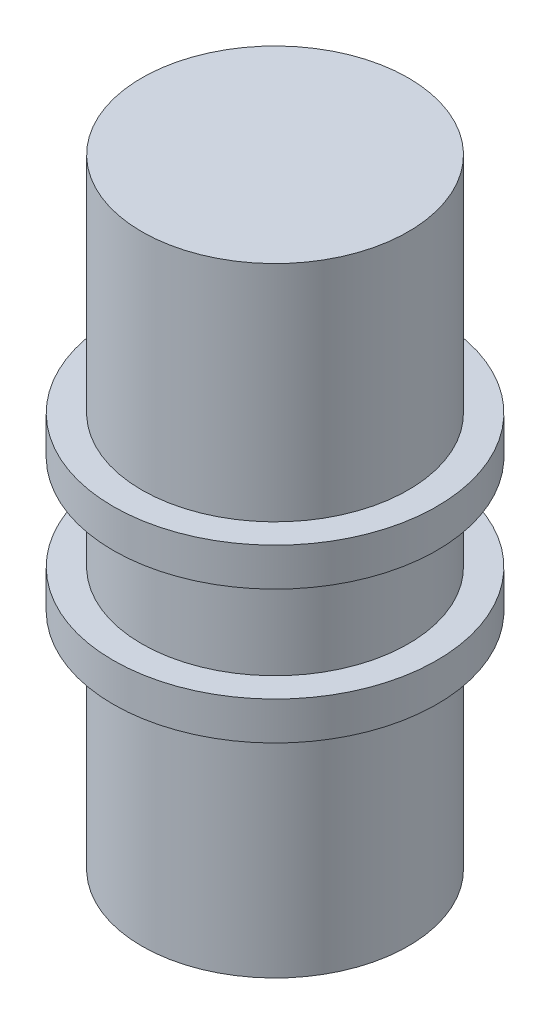
SolidWorks part; units mm, degrees
ref_plane "前视基准面" through (0, 0, 0) normal (0, 0, 1) x (1, 0, 0)
ref_plane "上视基准面" through (0, 0, 0) normal (0, 1, 0) x (1, 0, 0)
ref_plane "右视基准面" through (0, 0, 0) normal (1, 0, 0) x (0, 0, -1)
other "Configuration Table"
sketch "草图1" plane through (0, 0, 0) normal (0, 1, 0) x (1, 0, 0)
  circle A0 centre (0, 0) radius 7
  dimension "D1" = 14
extrude "凸台-拉伸1" add sketch "草图1" along normal mid plane 32.5
sketch "草图2" plane through (0, 0, 0) normal (0, 1, 0) x (1, 0, 0)
  circle A0 centre (0, 0) radius 8.5
  dimension "D1" = 17
extrude "凸台-拉伸2" add sketch "草图2" along normal blind 2 from offset 2.5
mirror "镜向1" about plane through (0, 0, 0) normal (0, 1, 0) of "凸台-拉伸2"
